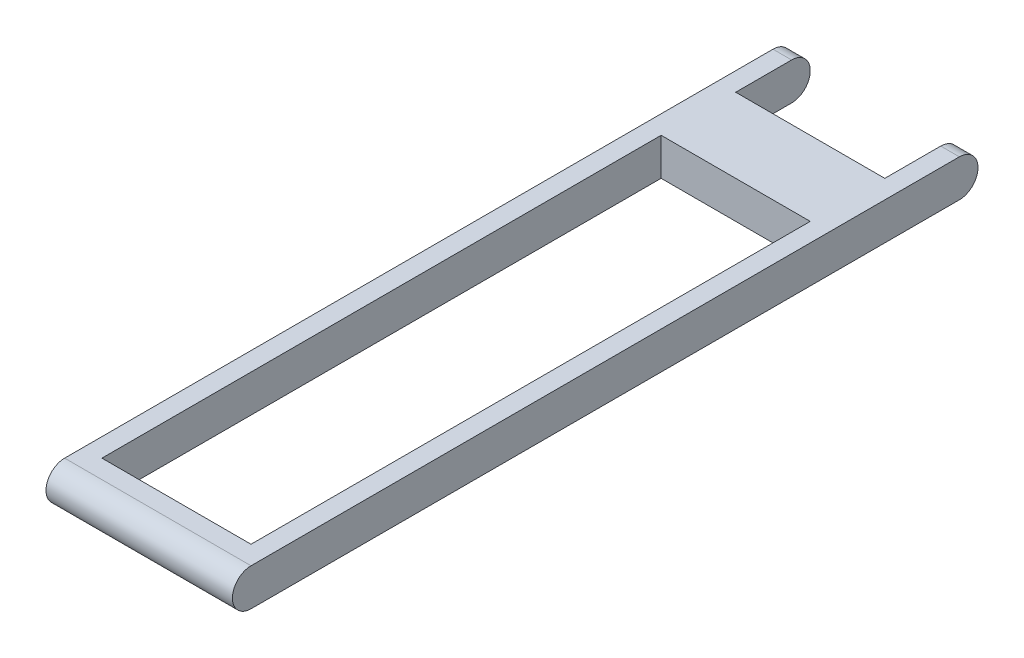
SolidWorks part; units mm, degrees
ref_plane "Front" through (0, 0, 0) normal (0, 0, 1) x (1, 0, 0)
ref_plane "Top" through (0, 0, 0) normal (0, 1, 0) x (1, 0, 0)
ref_plane "Right" through (0, 0, 0) normal (1, 0, 0) x (0, 0, -1)
sketch "草图1" plane through (0, 0, 0) normal (1, 0, 0) x (0, 0, -1)
  line L0 (-19, 0) -> (19, 0) construction
  line L1 (-19, 1) -> (19, 1)
  line L2 (-19, -1) -> (19, -1)
  arc A0 (-19, 1) -> (-19, -1) centre (-19, 0) ccw
  arc A1 (19, -1) -> (19, 1) centre (19, 0) ccw
  point P2 (0, 0)
extrude "凸台-拉伸1" add sketch "草图1" along normal blind 10
sketch "草图3" plane through (0, 1, 0) normal (0, 1, 0) x (1, 0, 0)
  line L0 (10, 20) -> (0, 20) construction
  line L1 (1, 12) -> (9, 12)
  line L2 (1, 12) -> (1, -18)
  line L3 (1, -18) -> (9, -18)
  line L4 (9, 12) -> (9, -18)
  line L5 (0, -20) -> (10, -20) construction
  line L7 (1, 23.5118) -> (9, 23.5118)
  line L8 (1, 23.5118) -> (1, 16)
  line L9 (1, 16) -> (9, 16)
  line L10 (9, 23.5118) -> (9, 16)
  dimension "D1" = 8
  dimension "D2" = 8
  dimension "D3" = 2
  dimension "D4" = 1
  dimension "D5" = 4
extrude "切除-拉伸2" cut sketch "草图3" against normal blind 10
